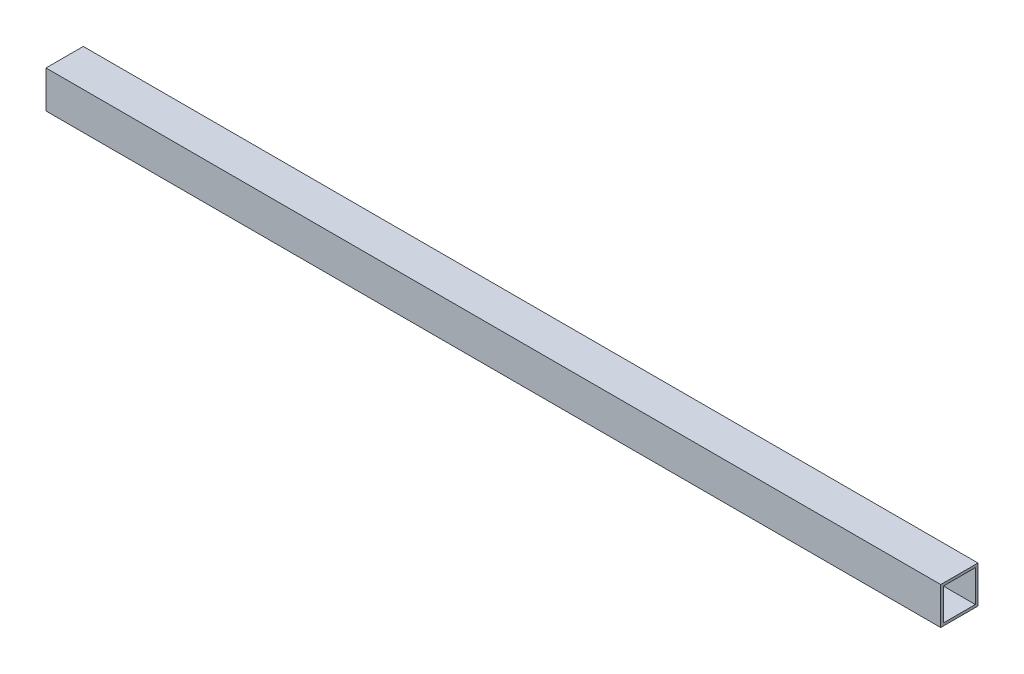
SolidWorks part; units mm, degrees
material "6061 Alloy"
ref_plane "Front Plane" through (0, 0, 0) normal (0, 0, 1) x (1, 0, 0)
ref_plane "Top Plane" through (0, 0, 0) normal (0, 1, 0) x (1, 0, 0)
ref_plane "Right Plane" through (0, 0, 0) normal (1, 0, 0) x (0, 0, -1)
sketch "Sketch1" plane through (0, 0, 0) normal (1, 0, 0) x (0, 0, -1)
  line L1 (0, 0) -> (44.45, 0)
  line L2 (0, 0) -> (0, 44.45)
  line L3 (0, 44.45) -> (44.45, 44.45)
  line L4 (44.45, 0) -> (44.45, 44.45)
  line L5 (3.175, 3.175) -> (41.275, 3.175)
  line L6 (3.175, 3.175) -> (3.175, 41.275)
  line L7 (3.175, 41.275) -> (41.275, 41.275)
  line L8 (41.275, 3.175) -> (41.275, 41.275)
  dimension "D1" = 44.45
  dimension "D2" = 44.45
  dimension "D3" = 38.1
  dimension "D4" = 3.175
  dimension "D5" = 3.175
  dimension "D6" = 38.1
extrude "Boss-Extrude1" add sketch "Sketch1" along normal blind 1066.8
sketch "Sketch2" plane through (0, 44.45, 0) normal (0, 1, 0) x (1, 0, 0)
  line L0 (1066.8, 44.45) -> (0, 44.45) construction
  line L2 (0, 44.45) -> (0, 0) construction
  line L3 (533.4, 0) -> (533.4, 44.45) construction
  line L4 (1066.8, 0) -> (0, 0) construction
  circle A0 centre (395.8158, 22.225) radius 2.4574
  circle A1 centre (120.65, 22.225) radius 2.4575
  circle A3 centre (670.9842, 22.225) radius 2.4574
  circle A4 centre (946.15, 22.225) radius 2.4575
  circle A5 centre (22.225, 22.225) radius 3.3734
  circle A6 centre (1044.575, 22.225) radius 3.3734
  dimension "D2" = 4.9149
  dimension "D9" = 6.7469
  dimension "D1" = 22.225
  dimension "D3" = 22.225
  dimension "D4" = 395.8158
  dimension "D5" = 120.65
  dimension "D6" = 44.45
  dimension "D7" = 22.225
  dimension "D8" = 22.225
extrude "Cut-Extrude1" [suppressed] cut sketch "Sketch2" against normal through all
sketch "Sketch3" plane through (0, 0, 0) normal (0, 0, 1) x (1, 0, 0)
  line L0 (0, 44.45) -> (0, 0) construction
  line L1 (1066.8, 44.45) -> (0, 44.45) construction
  line L2 (1066.8, 44.45) -> (1066.8, 0) construction
  circle A0 centre (120.65, 22.225) radius 2.4574
  circle A1 centre (395.8167, 22.225) radius 2.4575
  circle A2 centre (670.9833, 22.225) radius 2.4574
  circle A3 centre (946.15, 22.225) radius 2.4575
  circle A4 centre (22.225, 22.225) radius 3.3734
  circle A5 centre (1044.575, 22.225) radius 3.3734
  dimension "D3" = 4.9149
  dimension "D5" = 120.65
  dimension "D8" = 6.7469
  dimension "D11" = 6.7469
  dimension "D1" = 120.65
  dimension "D2" = 22.225
  dimension "D6" = 22.225
  dimension "D7" = 22.225
  dimension "D9" = 22.225
  dimension "D10" = 22.225
  dimension "D4" = 4
extrude "Cut-Extrude2" [suppressed] cut sketch "Sketch3" against normal through all
